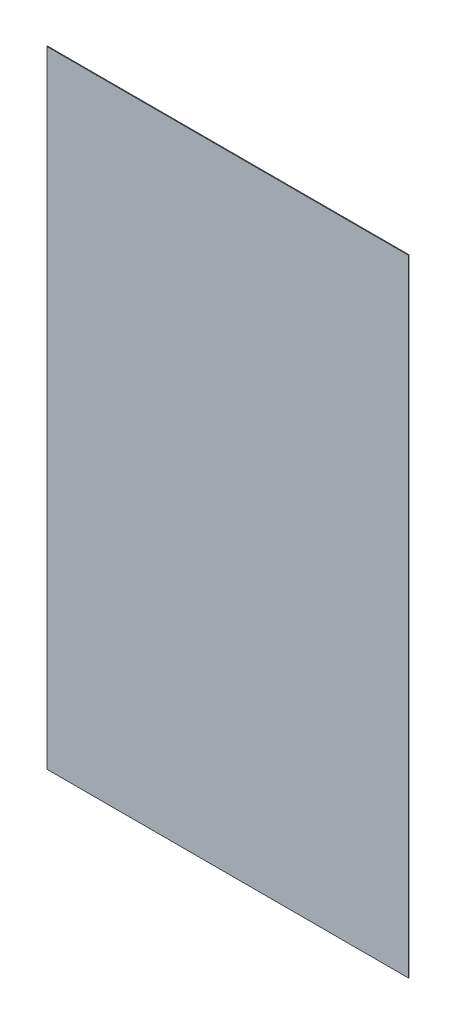
SolidWorks part; units mm, degrees
ref_plane "Front Plane" through (0, 0, 0) normal (0, 0, 1) x (1, 0, 0)
ref_plane "Top Plane" through (0, 0, 0) normal (0, 1, 0) x (1, 0, 0)
ref_plane "Right Plane" through (0, 0, 0) normal (1, 0, 0) x (0, 0, -1)
sketch "Sketch1" plane through (0, 0, 0) normal (0, 0, 1) x (1, 0, 0)
  line L1 (-203.25, 351.75) -> (203.25, 351.75)
  line L2 (-203.25, 351.75) -> (-203.25, -351.75)
  line L3 (-203.25, -351.75) -> (203.25, -351.75)
  line L4 (203.25, 351.75) -> (203.25, -351.75)
  line L5 (-203.25, 351.75) -> (203.25, -351.75) construction
  line L6 (-203.25, -351.75) -> (203.25, 351.75) construction
  point P0 (0, 0)
  dimension "D1" = 406.5
  dimension "D2" = 703.5
extrude "Boss-Extrude1" add sketch "Sketch1" along normal blind 0.85
